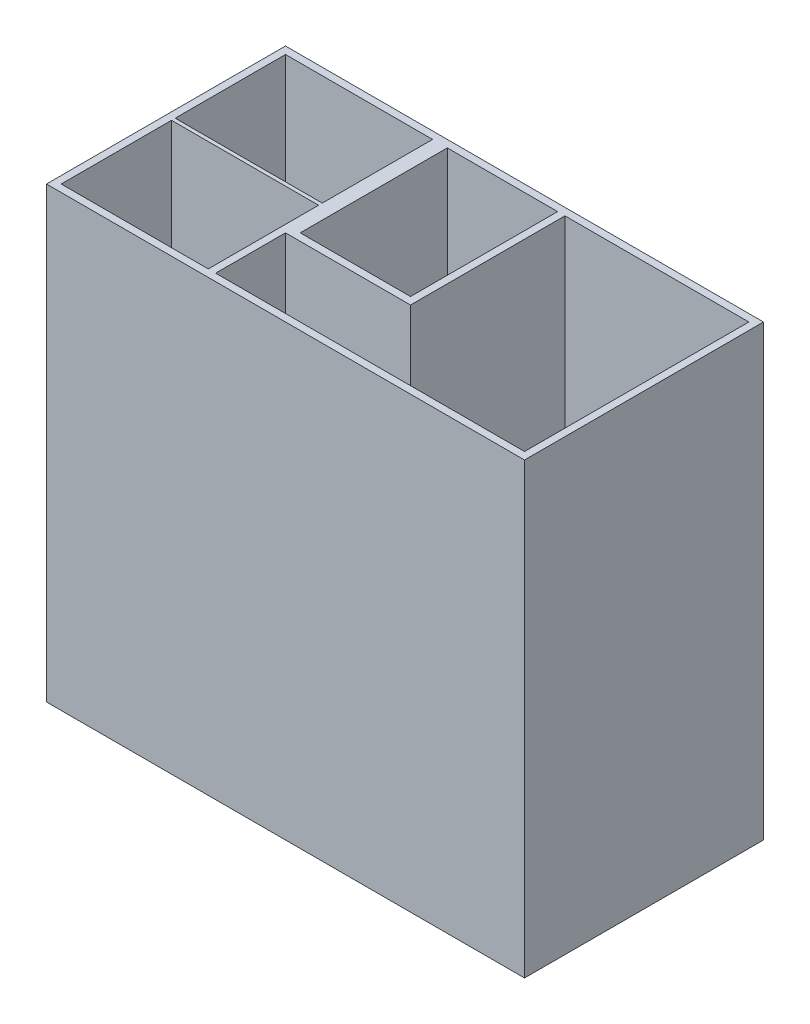
SolidWorks part; units mm, degrees
ref_plane "Front Plane" through (0, 0, 0) normal (0, 0, 1) x (1, 0, 0)
ref_plane "Top Plane" through (0, 0, 0) normal (0, 1, 0) x (1, 0, 0)
ref_plane "Right Plane" through (0, 0, 0) normal (1, 0, 0) x (0, 0, -1)
sketch "Sketch1" plane through (0, 0, 0) normal (0, 1, 0) x (1, 0, 0)
  line L1 (-65, 32.5) -> (65, 32.5)
  line L2 (-65, 32.5) -> (-65, -32.5)
  line L3 (-65, -32.5) -> (65, -32.5)
  line L4 (65, 32.5) -> (65, -32.5)
  line L5 (-65, 32.5) -> (65, -32.5) construction
  line L6 (-65, -32.5) -> (65, 32.5) construction
  point P0 (0, 0)
  dimension "D1" = 65
  dimension "D2" = 130
extrude "Boss-Extrude1" add sketch "Sketch1" along normal blind 2
sketch "Sketch2" plane through (0, 2, 0) normal (0, 1, 0) x (1, 0, 0)
  line L1 (-65, 32.5) -> (65, 32.5)
  line L2 (-65, 32.5) -> (-65, -32.5)
  line L3 (-65, -32.5) -> (65, -32.5)
  line L4 (65, 32.5) -> (65, -32.5)
  line L5 (-65, 32.5) -> (65, -32.5) construction
  line L6 (-65, -32.5) -> (65, 32.5) construction
  line L7 (-63, 30.5) -> (63, 30.5)
  line L8 (-63, 30.5) -> (-63, -30.5)
  line L9 (-63, -30.5) -> (63, -30.5)
  line L10 (63, 30.5) -> (63, -30.5)
  line L11 (-63, 30.5) -> (63, -30.5) construction
  line L12 (-63, -30.5) -> (63, 30.5) construction
  point P0 (0, 0)
  point P7 (0, 0)
  dimension "D1" = 2
  dimension "D2" = 2
extrude "Boss-Extrude2" add sketch "Sketch2" along normal blind 120
sketch "Sketch4" plane through (0, 2, 0) normal (0, 1, 0) x (1, 0, 0)
  line L0 (-23, 30.5) -> (-63, 30.5)
  line L1 (-63, 30.5) -> (63, 30.5)
  line L2 (-63, 30.5) -> (-63, -30.5)
  line L3 (-63, -30.5) -> (-21, -30.5)
  line L4 (63, 30.5) -> (63, -30.5)
  line L5 (63, 30.5) -> (13, 30.5)
  line L6 (63, 30.5) -> (63, -30.5)
  line L7 (13, -11.5) -> (-23, -11.5)
  line L8 (13, 30.5) -> (13, -11.5)
  line L9 (13, 30.5) -> (11, 30.5)
  line L10 (13, 30.5) -> (13, -11.5)
  line L11 (-21, -30.5) -> (-21, -11.5)
  line L12 (11, 30.5) -> (11, -9.5)
  line L13 (63, 30.5) -> (-63, 30.5)
  line L14 (63, 30.5) -> (63, -30.5)
  line L16 (-63, 30.5) -> (-63, -30.5)
  line L17 (-23, -0.5) -> (-63, -0.5)
  line L18 (-23, -0.5) -> (-23, -30.5)
  line L19 (-23, -30.5) -> (-63, -30.5)
  line L20 (-63, -0.5) -> (-63, -30.5)
  line L21 (-23, 30.5) -> (-23, 0.5)
  line L22 (-23, 0.5) -> (-63, 0.5)
  line L23 (-63, 30.5) -> (-63, 0.5)
  line L24 (11, -9.5) -> (13, -9.5)
  line L25 (-21, 30.5) -> (-23, 30.5)
  line L26 (11, -9.5) -> (-23, -9.5)
  line L27 (-21, -30.5) -> (-23, -30.5)
  line L28 (-23, 30.5) -> (-23, -30.5)
  line L29 (-19, 30.5) -> (11, 30.5)
  line L30 (-19, 30.5) -> (-19, -9.5)
  line L31 (-19, -9.5) -> (11, -9.5)
  line L32 (11, 30.5) -> (11, -9.5)
  line L35 (-23, -9.5) -> (-23, -11.5)
  line L37 (-21, -30.5) -> (-63, -30.5)
  dimension "D1" = 2
  dimension "D2" = 50
  dimension "D3" = 40
  dimension "D4" = 30
  dimension "D5" = 30
  dimension "D6" = 40
  dimension "D8" = 30
  dimension "D9" = 40
extrude "Boss-Extrude3" add sketch "Sketch4" along normal blind 120 contours L30 L13 L21 L28 L18 L26 | L28 L22 L16 L17 | L7 L18 L3 L11 | L24 L26 L18 L7 L10 | L12 L24 L8 L1
